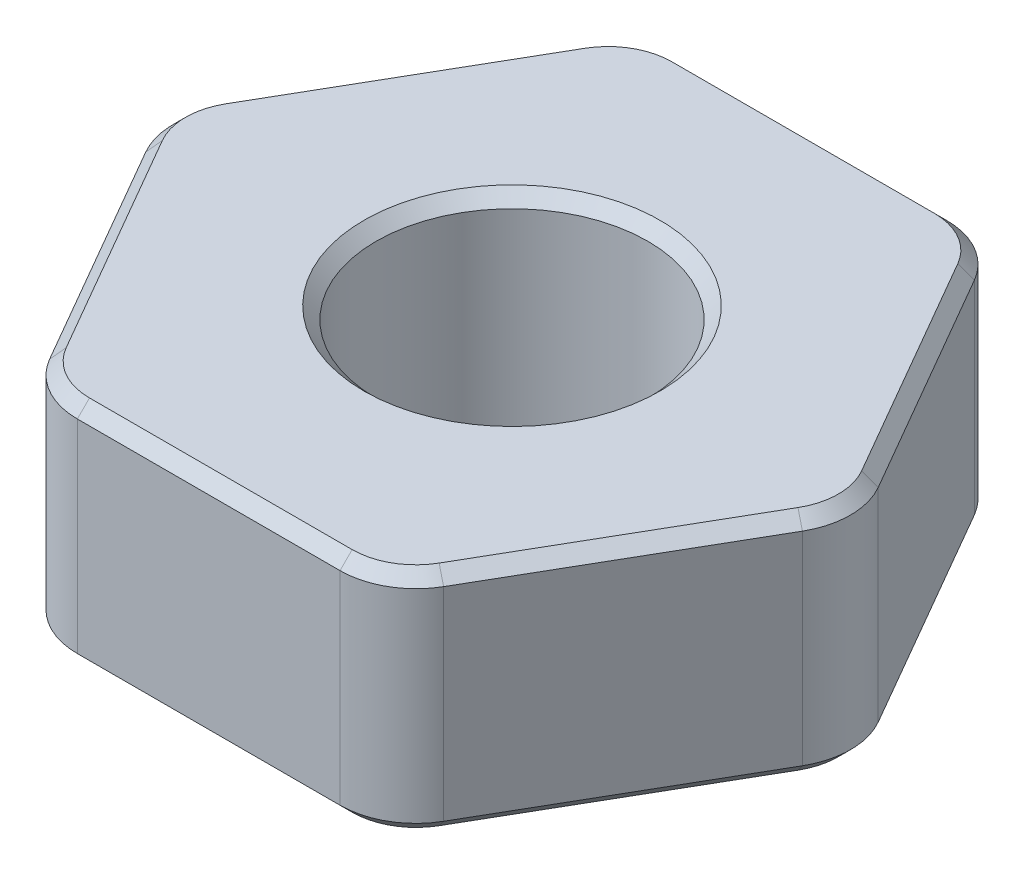
SolidWorks part; units mm, degrees
material "Alloy Steel"
ref_plane "Front Plane" through (0, 0, 0) normal (0, 0, 1) x (1, 0, 0)
ref_plane "Top Plane" through (0, 0, 0) normal (0, 1, 0) x (1, 0, 0)
ref_plane "Right Plane" through (0, 0, 0) normal (1, 0, 0) x (0, 0, -1)
sketch "Sketch3" plane through (0, 0, 0) normal (0, 1, 0) x (1, 0, 0)
  line L1 (1.8331, 3.175) -> (-1.8331, 3.175)
  line L2 (-1.8331, 3.175) -> (-3.6662, 0)
  line L3 (-3.6662, 0) -> (-1.8331, -3.175)
  line L4 (-1.8331, -3.175) -> (1.8331, -3.175)
  line L5 (1.8331, -3.175) -> (3.6662, 0)
  line L6 (3.6662, 0) -> (1.8331, 3.175)
  circle A0 centre (0, 0) radius 3.6662 construction
  circle A1 centre (0, 0) radius 1.4224
  circle A2 centre (0, 0) radius 3.175 construction
  dimension "D1" = 2.8448
  dimension "D2" = 6.35
extrude "Boss-Extrude1" add sketch "Sketch3" along normal mid plane 2.3813 contours L2 L3 L4 L5 L6 L1
fillet "Fillet1" radius 0.7937 6 edges at (3.6662, 0, 0) (1.8331, 0, 3.175) (-3.6662, 0, 0) (-1.8331, 0, -3.175) (1.8331, 0, -3.175) (-1.8331, 0, 3.175)
chamfer "Chamfer1" distance 0.127 angle 45 26 edges at (0, -1.1906, 1.4224) (0, 1.1906, 1.4224) (0, 1.1906, -3.175) (-1.7717, 1.1906, -3.0687) (1.7717, 1.1906, -3.0687) (-2.7496, 1.1906, -1.5875) (2.7496, 1.1906, -1.5875) (-3.5434, 1.1906, 0) (3.5434, 1.1906, 0) (-2.7496, 1.1906, 1.5875) (2.7496, 1.1906, 1.5875) (-1.7717, 1.1906, 3.0687) (1.7717, 1.1906, 3.0687) (0, 1.1906, 3.175) (0, -1.1906, -3.175) (-1.7717, -1.1906, -3.0687) (1.7717, -1.1906, -3.0687) (-2.7496, -1.1906, -1.5875) (2.7496, -1.1906, -1.5875) (-3.5434, -1.1906, 0) (3.5434, -1.1906, 0) (-2.7496, -1.1906, 1.5875) (2.7496, -1.1906, 1.5875) (-1.7717, -1.1906, 3.0687) (1.7717, -1.1906, 3.0687) (0, -1.1906, 3.175)
